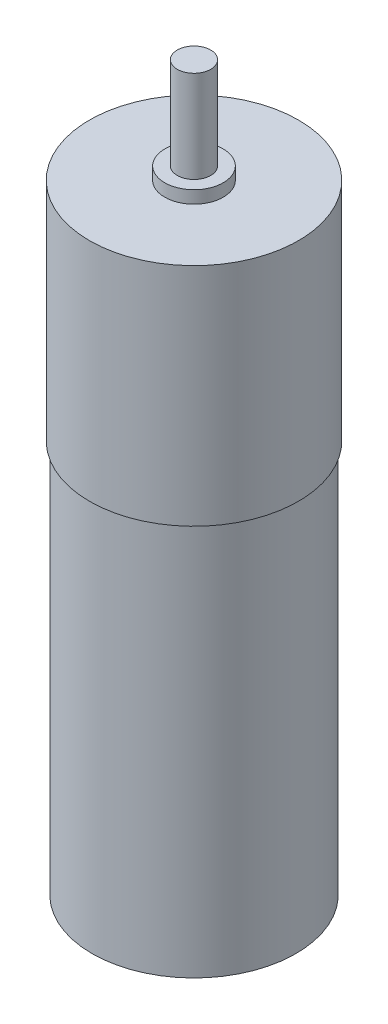
SolidWorks part; units mm, degrees
ref_plane "Front Plane" through (0, 0, 0) normal (0, 0, 1) x (1, 0, 0)
ref_plane "Top Plane" through (0, 0, 0) normal (0, 1, 0) x (1, 0, 0)
ref_plane "Right Plane" through (0, 0, 0) normal (1, 0, 0) x (0, 0, -1)
sketch "Sketch1" plane through (0, 0, 0) normal (0, 1, 0) x (1, 0, 0)
  circle A0 centre (0, 0) radius 12.2
  dimension "D1" = 24.4
extrude "Boss-Extrude1" add sketch "Sketch1" along normal mid plane 47
sketch "Sketch2" plane through (0, 23.5, 0) normal (0, 1, 0) x (1, 0, 0)
  circle A0 centre (0, 0) radius 12.5
  dimension "D1" = 25
extrude "Boss-Extrude2" add sketch "Sketch2" along normal blind 27
sketch "Sketch3" plane through (0, 50.5, 0) normal (0, 1, 0) x (1, 0, 0)
  circle A0 centre (0, 0) radius 3.5
  dimension "D1" = 7
extrude "Boss-Extrude3" add sketch "Sketch3" along normal blind 1.5
sketch "Sketch4" plane through (0, 52, 0) normal (0, 1, 0) x (1, 0, 0)
  circle A0 centre (0, 0) radius 2
  dimension "D1" = 4
extrude "Boss-Extrude4" add sketch "Sketch4" along normal blind 11
